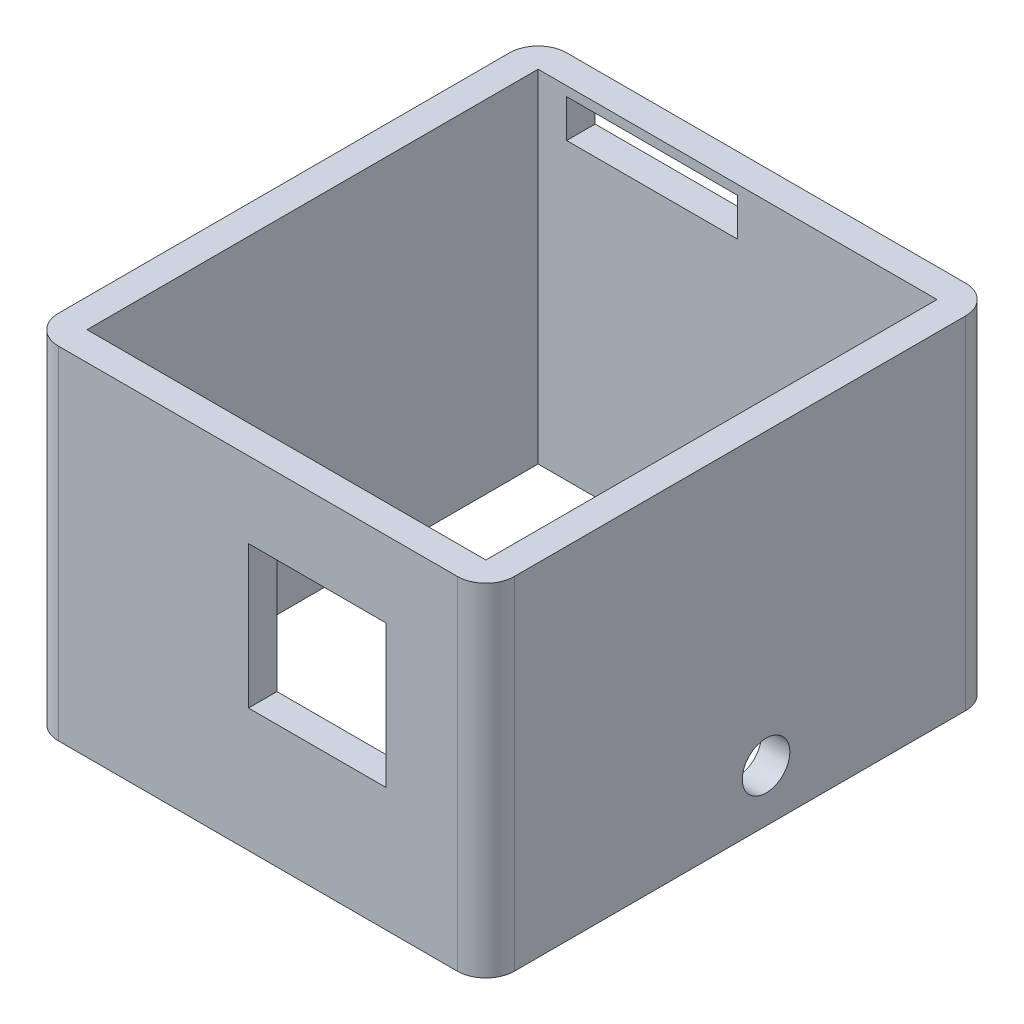
SolidWorks part; units mm, degrees
ref_plane "Front Plane" through (0, 0, 0) normal (0, 0, 1) x (1, 0, 0)
ref_plane "Top Plane" through (0, 0, 0) normal (0, 1, 0) x (1, 0, 0)
ref_plane "Right Plane" through (0, 0, 0) normal (1, 0, 0) x (0, 0, -1)
sketch "Sketch1" plane through (0, 0, 0) normal (0, 1, 0) x (1, 0, 0)
  line L1 (-24, -26.75) -> (24, -26.75)
  line L2 (-24, -26.75) -> (-24, 26.75)
  line L3 (-24, 26.75) -> (24, 26.75)
  line L4 (24, -26.75) -> (24, 26.75)
  line L5 (-24, -26.75) -> (24, 26.75) construction
  line L6 (-24, 26.75) -> (24, -26.75) construction
  line L7 (-21, -23.75) -> (21, -23.75)
  line L8 (-21, -23.75) -> (-21, 23.75)
  line L9 (-21, 23.75) -> (21, 23.75)
  line L10 (21, -23.75) -> (21, 23.75)
  line L11 (-21, -23.75) -> (21, 23.75) construction
  line L12 (-21, 23.75) -> (21, -23.75) construction
  point P0 (0, 0)
  point P6 (0, 0)
  dimension "D1" = 48
  dimension "D2" = 53.5
  dimension "D3" = 42
  dimension "D4" = 47.5
extrude "Boss-Extrude1" add sketch "Sketch1" along normal blind 36
ref_plane "Plane1" through (0, 0, 23.75) normal (0, 0, 1) x (1, 0, 0)
ref_plane "Plane2" through (0, 0, -23.75) normal (0, 0, 1) x (1, 0, 0)
ref_plane "Plane3" through (0, 0, -0.25) normal (0, 0, 1) x (1, 0, 0)
ref_plane "Plane4" through (0, 0, -5.25) normal (0, 0, 1) x (1, 0, 0)
ref_plane "Plane5" through (21, 0, 0) normal (1, 0, 0) x (0, 0, -1)
ref_plane "Plane6" through (0, 1, 0) normal (0, 1, 0) x (1, 0, 0)
ref_plane "Plane7" through (0, 8, 0) normal (0, 1, 0) x (1, 0, 0)
ref_plane "Plane8" through (0, 9, 0) normal (0, 1, 0) x (1, 0, 0)
ref_plane "Plane9" through (0, 28, 0) normal (0, 1, 0) x (1, 0, 0)
ref_plane "Plane10" through (0, 31, 0) normal (0, 1, 0) x (1, 0, 0)
ref_plane "Plane11" through (0, 36, 0) normal (0, 1, 0) x (1, 0, 0)
ref_plane "Plane12" through (0, 3, 0) normal (0, 1, 0) x (1, 0, 0)
sketch "Sketch2" plane through (21, 0, 0) normal (1, 0, 0) x (0, 0, -1)
  line L0 (26.4, 3) -> (-26.4, 3) construction
  line L1 (0.25, 19.8) -> (0.25, -19.8) construction
  line L2 (26.4, 8) -> (-26.4, 8) construction
  line L3 (5.25, 19.8) -> (5.25, -19.8) construction
  line L4 (-4.3054, 5.5) -> (12.9138, 5.5) construction
  line L9 (2.75, 12.4847) -> (2.75, 4.3497) construction
  circle A0 centre (2.75, 5.5) radius 2.5
  point P0 (0.25, 3)
  point P1 (0.25, 8)
  point P6 (5.25, 8)
  point P9 (5.25, 3)
  point P17 (0.25, 5.5)
  point P19 (5.25, 5.5)
  point P22 (2.75, 5.5)
  dimension "D1" = 2.5
  dimension "D2" = 2.5
extrude "Cut-Extrude1" cut sketch "Sketch2" along normal blind 9
ref_plane "Plane13" through (13.5, 0, 0) normal (1, 0, 0) x (0, 0, -1)
ref_plane "Plane14" through (-1, 0, 0) normal (1, 0, 0) x (0, 0, -1)
ref_plane "Plane15" through (0, 13, 0) normal (0, 1, 0) x (1, 0, 0)
sketch "Sketch3" plane through (0, 0, 23.75) normal (0, 0, 1) x (1, 0, 0)
  line L0 (-6.9905, 28) -> (35.6025, 28) construction
  line L2 (-4.9313, 13) -> (36.6321, 13) construction
sketch "Sketch4" plane through (0, 0, 23.75) normal (0, 0, 1) x (1, 0, 0)
  line L0 (-1, 22.1455) -> (-1, 39.8113) construction
  line L2 (13.5, 33.146) -> (13.5, 41.3828) construction
  line L4 (-200006.9905, 28) -> (200035.6025, 28) construction
  line L5 (-200004.9313, 13) -> (200036.6321, 13) construction
  line L7 (-1, 13) -> (13.5, 13)
  line L8 (-1, 13) -> (-1, 28)
  line L9 (-1, 28) -> (13.5, 28)
  line L10 (13.5, 13) -> (13.5, 28)
  point P2 (-1, 28)
  point P3 (13.5, 28)
  point P5 (13.5, 13)
  point P9 (-1, 13)
extrude "Cut-Extrude2" cut sketch "Sketch4" along normal blind 15
ref_plane "Plane16" through (-21, 0, 0) normal (1, 0, 0) x (0, 0, -1)
ref_plane "Plane17" through (-18, 0, 0) normal (1, 0, 0) x (0, 0, -1)
ref_plane "Plane19" through (0, 35, 0) normal (0, 1, 0) x (1, 0, 0)
sketch "Sketch6" plane through (0, 0, -23.75) normal (0, 0, 1) x (1, 0, 0)
  line L0 (-6.3115, 35) -> (-27.4226, 35) construction
  line L2 (-10.3447, 31) -> (-27.6957, 31) construction
  line L4 (0, 32.6752) -> (0, 40.6975) construction
  line L6 (-18, 29.2206) -> (-18, 39.0695) construction
  line L9 (0, 31) -> (-18, 31)
  line L10 (0, 31) -> (0, 35)
  line L11 (0, 35) -> (-18, 35)
  line L12 (-18, 31) -> (-18, 35)
  point P3 (0, 31)
  point P6 (0, 35)
  point P9 (-18, 35)
  point P12 (-18, 31)
extrude "Cut-Extrude3" cut sketch "Sketch6" against normal blind 15
ref_plane "Plane20" through (0, 0, 0) normal (0, 1, 0) x (1, 0, 0)
ref_plane "Plane21" through (0, 10, 0) normal (0, 1, 0) x (1, 0, 0)
ref_plane "Plane22" through (0, 15, 0) normal (0, 1, 0) x (1, 0, 0)
ref_plane "Plane23" through (0, 0, 15) normal (0, 0, 1) x (1, 0, 0)
ref_plane "Plane24" through (0, 0, 12) normal (0, 0, 1) x (1, 0, 0)
ref_plane "Plane25" through (0, 0, -15) normal (0, 0, 1) x (1, 0, 0)
ref_plane "Plane26" through (0, 0, -12) normal (0, 0, 1) x (1, 0, 0)
sketch "Sketch7" plane through (21, 0, 0) normal (1, 0, 0) x (0, 0, -1)
  line L0 (-15, 19.8) -> (-15, -19.8) construction
  line L1 (-15, 10) -> (-12, 10)
  line L2 (-15, 10) -> (-15, 15)
  line L3 (-15, 15) -> (-12, 15)
  line L4 (-12, 10) -> (-12, 15)
  line L5 (26.4, 10) -> (-26.4, 10) construction
  line L6 (-12, 19.8) -> (-12, -19.8) construction
  line L7 (12, 19.8) -> (12, -19.8) construction
  line L8 (12, 10) -> (15, 10)
  line L9 (12, 10) -> (12, 15)
  line L10 (12, 15) -> (15, 15)
  line L11 (15, 10) -> (15, 15)
  line L12 (15, 19.8) -> (15, -19.8) construction
ref_plane "Plane27" through (24, 0, 0) normal (1, 0, 0) x (0, 0, -1)
sketch "Sketch8" plane through (24, 0, 0) normal (1, 0, 0) x (0, 0, -1)
  line L0 (26.4, 15) -> (-26.4, 15) construction
  line L1 (-15, 10) -> (-12, 10)
  line L2 (-15, 10) -> (-15, 15)
  line L3 (-15, 15) -> (-12, 15)
  line L4 (-12, 10) -> (-12, 15)
  line L5 (12, 10) -> (15, 10)
  line L6 (12, 10) -> (12, 15)
  line L7 (12, 15) -> (15, 15)
  line L8 (15, 10) -> (15, 15)
ref_plane "Plane28" through (-24, 0, 0) normal (1, 0, 0) x (0, 0, -1)
sketch "Sketch9" plane through (-24, 0, 0) normal (1, 0, 0) x (0, 0, -1)
  line L1 (15, 15) -> (12, 15)
  line L2 (15, 15) -> (15, 10)
  line L3 (15, 10) -> (12, 10)
  line L4 (12, 15) -> (12, 10)
  line L5 (-12, 15) -> (-15, 15)
  line L6 (-12, 15) -> (-12, 10)
  line L7 (-12, 10) -> (-15, 10)
  line L8 (-15, 15) -> (-15, 10)
fillet "Fillet1" radius 3 4 edges at (24, 18, 26.75) (-24, 18, 26.75) (-24, 18, -26.75) (24, 18, -26.75)
